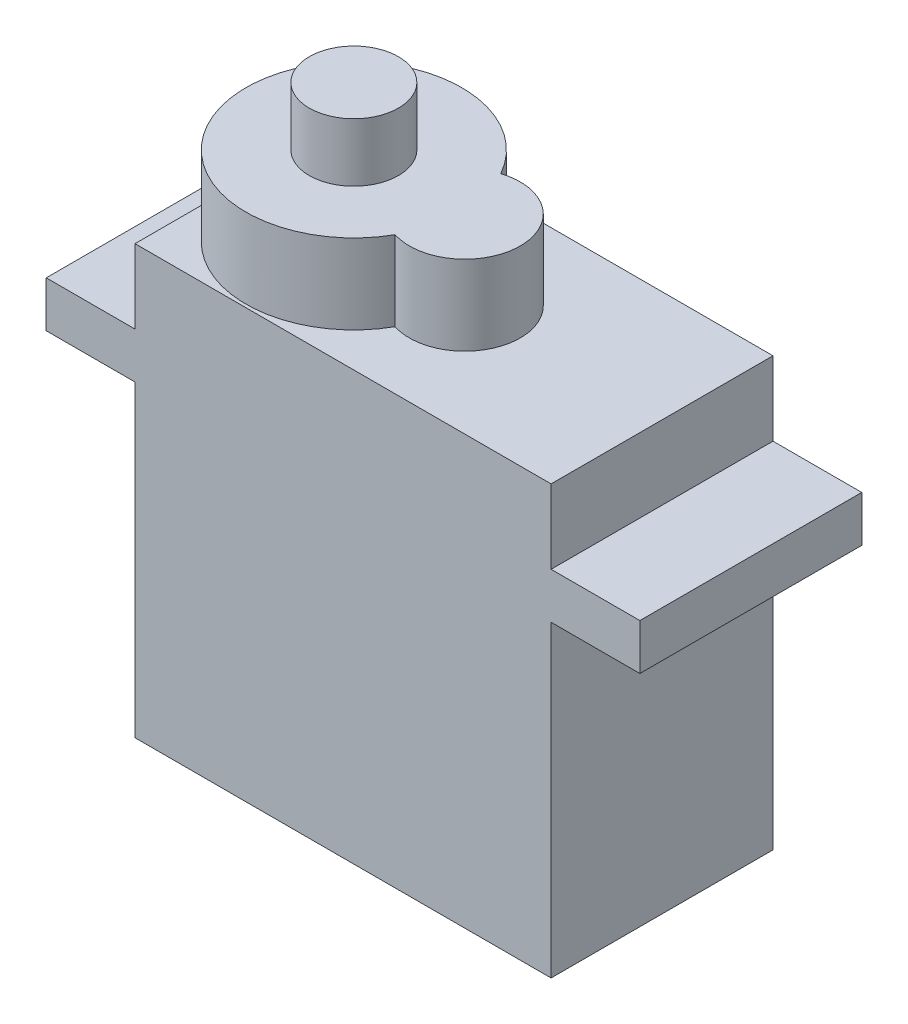
SolidWorks part; units mm, degrees
ref_plane "Front" through (0, 0, 0) normal (0, 0, 1) x (1, 0, 0)
ref_plane "Top" through (0, 0, 0) normal (0, 1, 0) x (1, 0, 0)
ref_plane "Right" through (0, 0, 0) normal (1, 0, 0) x (0, 0, -1)
sketch "Sketch1" plane through (0, 0, 0) normal (0, 1, 0) x (1, 0, 0)
  line L1 (0, 0) -> (22.5, 0)
  line L2 (0, 0) -> (0, 12)
  line L3 (0, 12) -> (22.5, 12)
  line L4 (22.5, 0) -> (22.5, 12)
  dimension "D1" = 22.5
  dimension "D2" = 12
extrude "Boss-Extrude1" add sketch "Sketch1" along normal blind 16.66
sketch "Sketch2" plane through (0, 16.66, 0) normal (0, 1, 0) x (1, 0, 0)
  line L0 (0, 12) -> (0, 0) construction
  line L1 (-4.8, 12) -> (27.3, 12)
  line L2 (-4.8, 12) -> (-4.8, 0)
  line L3 (-4.8, 0) -> (27.3, 0)
  line L4 (27.3, 12) -> (27.3, 0)
  line L5 (22.5, 0) -> (22.5, 12) construction
  line L6 (22.5, 12) -> (0, 12) construction
  line L7 (0, 0) -> (22.5, 0) construction
  dimension "D1" = 4.8
  dimension "D2" = 4.8
extrude "Boss-Extrude2" add sketch "Sketch2" along normal blind 2.48
sketch "Sketch3" plane through (0, 19.14, 0) normal (0, 1, 0) x (1, 0, 0)
  line L4 (0, 12) -> (0, 0)
  line L5 (22.5, 12) -> (0, 12)
  line L6 (22.5, 0) -> (22.5, 12)
  line L7 (0, 0) -> (22.5, 0)
  line L8 (0, 12) -> (0, 0)
  line L9 (22.5, 12) -> (0, 12)
  line L10 (22.5, 0) -> (22.5, 12)
  line L11 (0, 0) -> (22.5, 0)
  dimension "D1" = 0
extrude "Boss-Extrude3" add sketch "Sketch3" along normal blind 4
sketch "Sketch4" plane through (0, 23.14, 0) normal (0, 1, 0) x (1, 0, 0)
  line L0 (0, 12) -> (0, 0) construction
  arc A0 (10.9223, 8.8578) -> (10.9223, 3.1422) centre (5.835, 6) ccw
  arc A1 (10.9223, 3.1422) -> (10.9223, 8.8578) centre (11.835, 6) ccw
  dimension "D1" = 11.67
  dimension "D3" = 6
  dimension "D2" = 6
extrude "Boss-Extrude4" add sketch "Sketch4" along normal blind 4.31
sketch "Sketch5" plane through (0, 27.45, 0) normal (0, 1, 0) x (1, 0, 0)
  circle A0 centre (5.835, 6) radius 2.41
  dimension "D1" = 4.82
extrude "Boss-Extrude5" add sketch "Sketch5" along normal blind 3.16
sketch "Sketch6" plane through (0, 0, 0) normal (-1, 0, 0) x (0, 0, 1)
  line L0 (-12, 0) -> (0, 0) construction
  line L1 (-7.75, 4.1) -> (-4.25, 4.1)
  line L2 (-7.75, 4.1) -> (-7.75, 5.3)
  line L3 (-7.75, 5.3) -> (-4.25, 5.3)
  line L4 (-4.25, 4.1) -> (-4.25, 5.3)
  point P6 (-6, 0)
  point P7 (-6, 4.1)
  dimension "D1" = 3.5
  dimension "D2" = 1.2
  dimension "D3" = 5.3
extrude "Boss-Extrude6" add sketch "Sketch6" along normal blind 3 draft 3
